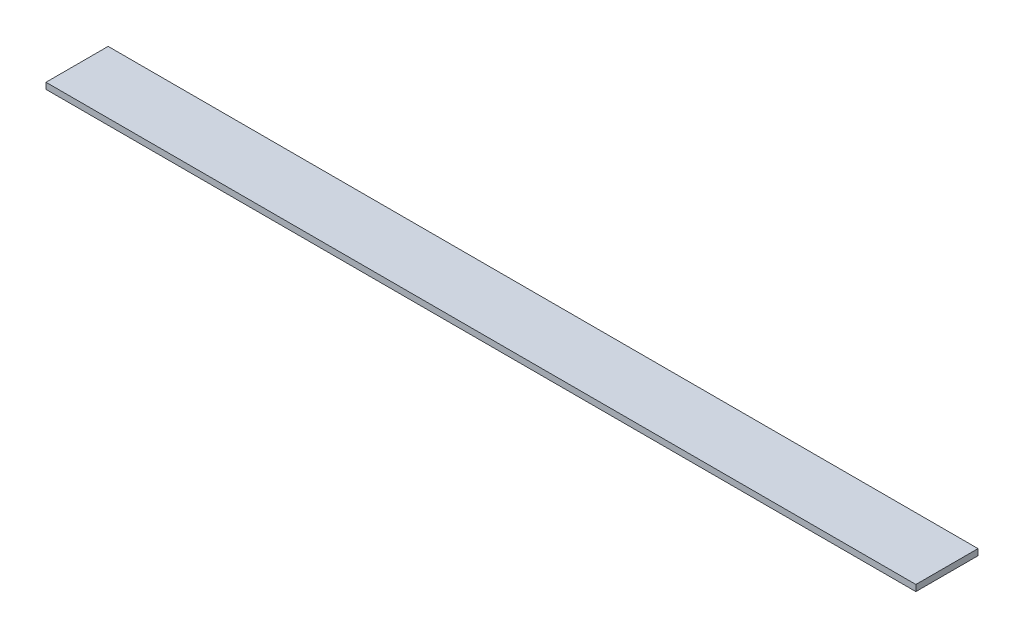
SolidWorks part; units mm, degrees
ref_plane "Face" through (0, 0, 0) normal (0, 0, 1) x (1, 0, 0)
ref_plane "Dessus" through (0, 0, 0) normal (0, 1, 0) x (1, 0, 0)
ref_plane "Droite" through (0, 0, 0) normal (1, 0, 0) x (0, 0, -1)
sketch "Esquisse1" plane through (0, 0, 0) normal (0, 1, 0) x (1, 0, 0)
  line L1 (0, 0) -> (1400, 0)
  line L2 (0, 0) -> (0, 100)
  line L3 (0, 100) -> (1400, 100)
  line L4 (1400, 0) -> (1400, 100)
  dimension "D1" = 1400
  dimension "D2" = 100
extrude "Extrusion1" add sketch "Esquisse1" along normal blind 10
